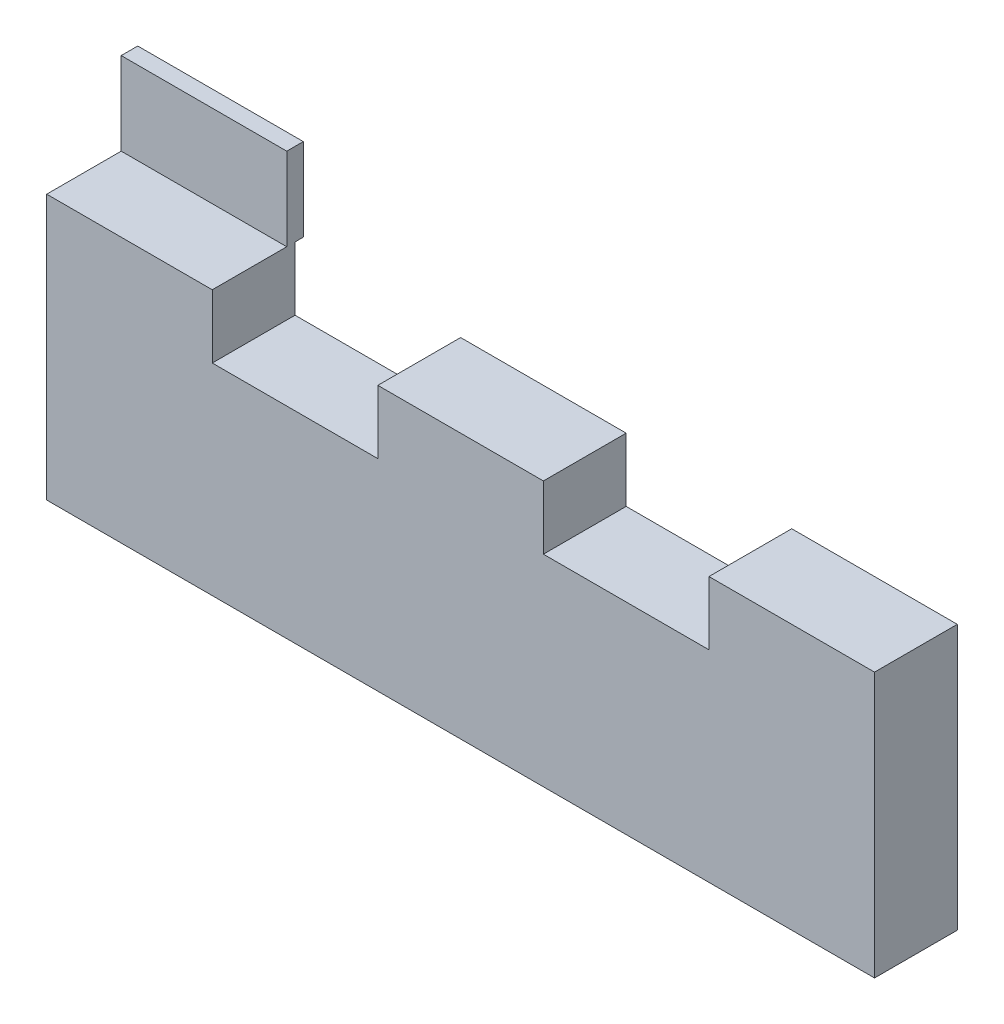
SolidWorks part; units mm, degrees
material "Stainless Steel"
ref_plane "Front Plane" through (0, 0, 0) normal (0, 0, 1) x (1, 0, 0)
ref_plane "Top Plane" through (0, 0, 0) normal (0, 1, 0) x (1, 0, 0)
ref_plane "Right Plane" through (0, 0, 0) normal (1, 0, 0) x (0, 0, -1)
sketch "Sketch1" plane through (0, 0, 0) normal (0, 0, 1) x (1, 0, 0)
  line L0 (0, 0) -> (0, 32)
  line L1 (0, 32) -> (20, 32)
  line L2 (20, 32) -> (20, 24.3353)
  line L3 (20, 24.3353) -> (40, 24.3353)
  line L4 (40, 24.3353) -> (40, 32)
  line L5 (40, 32) -> (60, 32)
  line L6 (60, 32) -> (60, 24.3353)
  line L7 (60, 24.3353) -> (80, 24.3353)
  line L8 (80, 24.3353) -> (80, 32)
  line L9 (80, 32) -> (100, 32)
  line L10 (100, 32) -> (100, 0)
  line L11 (100, 0) -> (0, 0)
  dimension "D1" = 32
  dimension "D2" = 100
  dimension "D3" = 20
  dimension "D4" = 20
  dimension "D5" = 20
  dimension "D6" = 20
extrude "Boss-Extrude2" add sketch "Sketch1" along normal blind 10
sketch "Sketch2" plane through (0, 32, 0) normal (0, 1, 0) x (1, 0, 0)
  line L1 (0, -1) -> (20, -1)
  line L2 (0, -1) -> (0, 1)
  line L3 (0, 1) -> (20, 1)
  line L4 (20, -1) -> (20, 1)
  point P5 (0, 0)
extrude "Boss-Extrude4" add sketch "Sketch2" along normal blind 10
sketch "Sketch4" plane through (0, 0, 0) normal (1, 0, 0) x (0, 0, -1)
  line L0 (-1, 42) -> (-20.0186, 42) construction
  line L2 (-10.5093, 42) -> (-12.5093, 42)
  line L3 (1, 42) -> (-1, 42)
  arc A0 (-10.5093, 42) -> (-1, 42) centre (-5.7546, 43.547) cw
  arc A1 (1, 42) -> (-12.5093, 42) centre (-5.7546, 43.837) ccw
  dimension "D1" = 2
  dimension "D3" = 5
  dimension "D4" = 7
  dimension "D2" = 2
